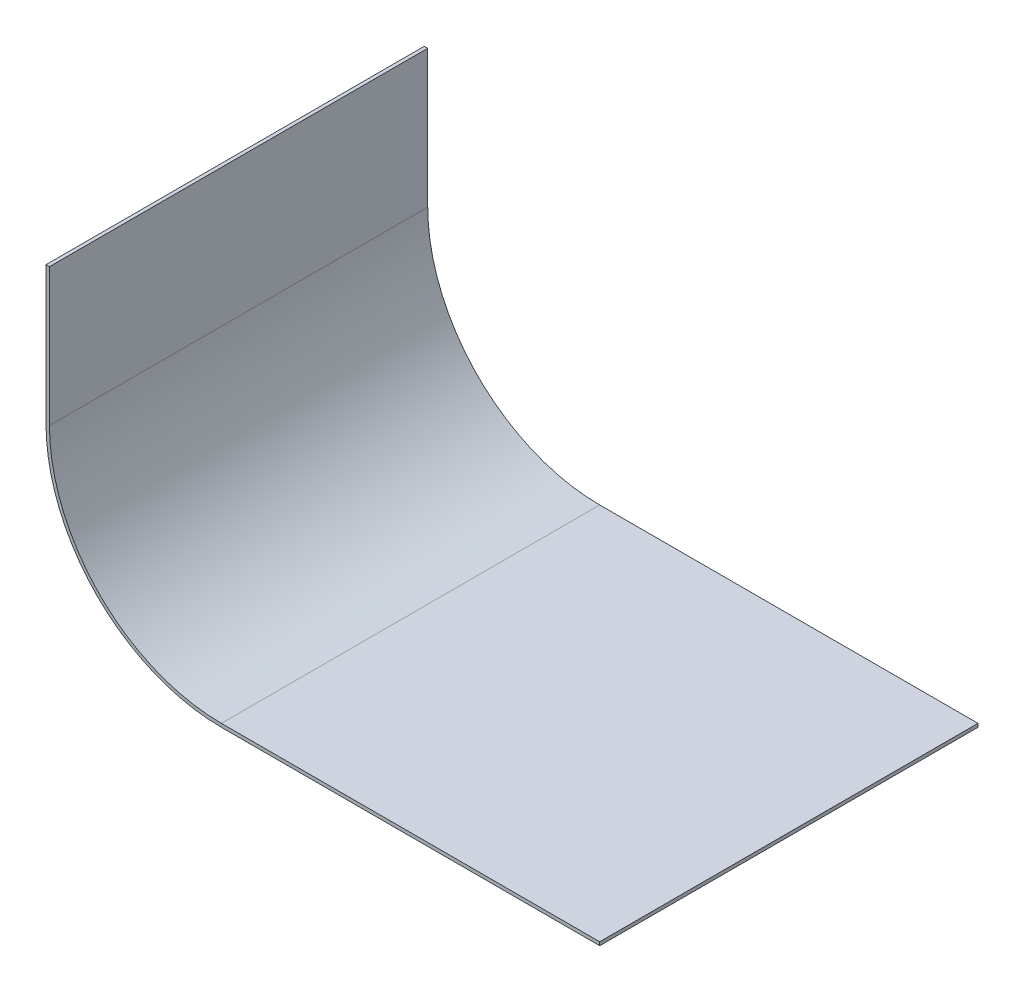
SolidWorks part; units mm, degrees
ref_plane "Front Plane" through (0, 0, 0) normal (0, 0, 1) x (1, 0, 0)
ref_plane "Top Plane" through (0, 0, 0) normal (0, 1, 0) x (1, 0, 0)
ref_plane "Right Plane" through (0, 0, 0) normal (1, 0, 0) x (0, 0, -1)
sketch "Sketch1" plane through (0, 0, 0) normal (0, 0, 1) x (1, 0, 0)
  line L0 (0, 0) -> (0, -4)
  line L1 (5, -9) -> (16, -9)
  line L2 (-0.1, 0) -> (-0.1, -4)
  line L3 (5, -9.1) -> (16, -9.1)
  line L4 (-0.1, 0) -> (0, 0)
  line L5 (16, -9) -> (16, -9.1)
  arc A0 (0, -4) -> (5, -9) centre (5, -4) ccw
  arc A1 (-0.1, -4) -> (5, -9.1) centre (5, -4) ccw
  dimension "D2" = 5
  dimension "D1" = 4
  dimension "D3" = 11
  dimension "D4" = 0.1
extrude "Boss-Extrude1" add sketch "Sketch1" along normal blind 11
